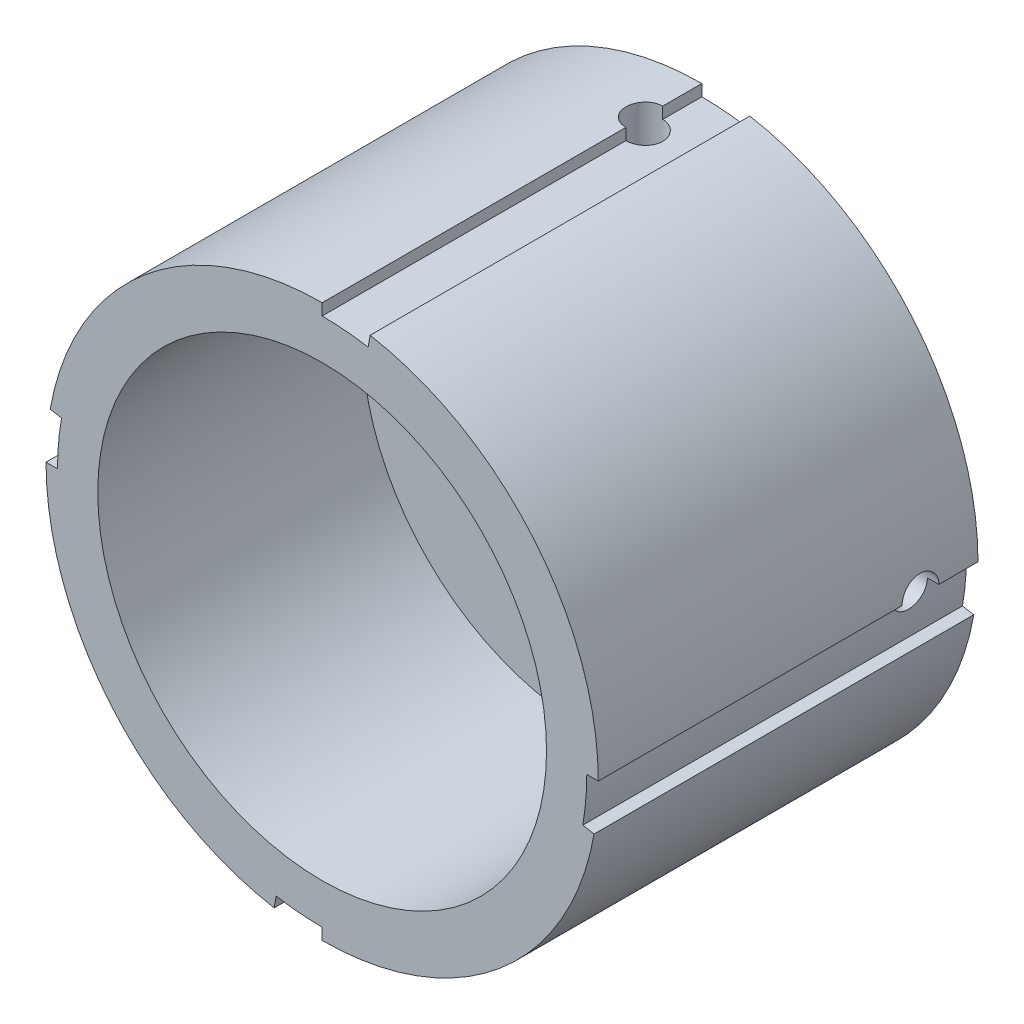
SolidWorks part; units mm, degrees
ref_plane "Alzado" through (0, 0, 0) normal (0, 0, 1) x (1, 0, 0)
ref_plane "Planta" through (0, 0, 0) normal (0, 1, 0) x (1, 0, 0)
ref_plane "Vista lateral" through (0, 0, 0) normal (1, 0, 0) x (0, 0, -1)
sketch "Croquis1" plane through (0, 0, 0) normal (0, 0, 1) x (1, 0, 0)
  line L0 (0, 0) -> (0, 24) construction
  line L1 (0, 24) -> (0, 23)
  line L2 (3.9939, 22.6506) -> (4.1676, 23.6354)
  line L3 (24, 0) -> (23, 0)
  line L4 (22.6506, -3.9939) -> (23.6354, -4.1676)
  line L5 (0, -24) -> (0, -23)
  line L6 (-3.9939, -22.6506) -> (-4.1676, -23.6354)
  line L7 (-24, 0) -> (-23, 0)
  line L8 (-22.6506, 3.9939) -> (-23.6354, 4.1676)
  line L9 (0, 0) -> (3.9939, 22.6506) construction
  arc A1 (3.9939, 22.6506) -> (0, 23) centre (0, 0) ccw
  arc A3 (22.6506, -3.9939) -> (23, 0) centre (0, 0) ccw
  arc A5 (-3.9939, -22.6506) -> (0, -23) centre (0, 0) ccw
  arc A7 (-22.6506, 3.9939) -> (-23, 0) centre (0, 0) ccw
  arc A8 (0, 24) -> (-23.6354, 4.1676) centre (0, 0) ccw
  arc A9 (24, 0) -> (4.1676, 23.6354) centre (0, 0) ccw
  arc A10 (0, -24) -> (23.6354, -4.1676) centre (0, 0) ccw
  arc A11 (-24, 0) -> (-4.1676, -23.6354) centre (0, 0) ccw
  circle A12 centre (0, 0) radius 23 construction
  point P20 (0, 0)
  dimension "D1" = 24
  dimension "D2" = 46
  dimension "D6" = 46
  dimension "D3" = 10
  dimension "D5" = 4
extrude "Saliente-Extruir1" add sketch "Croquis1" along normal mid plane 33
sketch "Croquis2" plane through (0, 0, 16.5) normal (0, 0, 1) x (1, 0, 0)
  circle A0 centre (0, 0) radius 19.5
  dimension "D1" = 39
extrude "Cortar-Extruir1" cut sketch "Croquis2" against normal blind 23
sketch "Croquis3" plane through (0, 0, -16.5) normal (0, 0, -1) x (-1, 0, 0)
  line L0 (-1.0308, 2) -> (1.0308, 2)
  circle A0 centre (0, 0) radius 2.25
  dimension "D1" = 4.5
  dimension "D2" = 2
extrude "Cortar-Extruir2" cut sketch "Croquis3" against normal blind 23 contours L0 A0
sketch "Croquis4" plane through (0, 0, 0) normal (0, 1, 0) x (1, 0, 0)
  line L0 (0, -20.7543) -> (0, 35.0478) construction
  line L1 (0, -16.5) -> (0, 16.5) construction
  line L2 (0, 16.5) -> (-23.6354, 16.5) construction
  circle A0 centre (0, 11.5) radius 1.6
  dimension "D1" = 3.2
  dimension "D2" = 5
extrude "Cortar-Extruir3" cut sketch "Croquis4" against normal mid plane 73
sketch "Croquis5" plane through (0, 0, 0) normal (1, 0, 0) x (0, 0, -1)
  line L0 (0, 0) -> (11.5, 0) construction
  line L1 (16.5, 0) -> (16.5, 23.6354) construction
  circle A0 centre (11.5, 0) radius 1.6
  dimension "D2" = 3.2
  dimension "D1" = 5
extrude "Cortar-Extruir4" cut sketch "Croquis5" against normal mid plane 283
sketch "Croquis6" plane through (0, 0, -16.5) normal (0, 0, -1) x (-1, 0, 0)
  line L0 (0, -25.9532) -> (0, 54.6675) construction
  line L1 (56.1694, 0) -> (-55.2683, 0) construction
  line L3 (-2.75, 9.4) -> (2.75, 9.4)
  line L4 (-2.75, 9.4) -> (-2.75, 7)
  line L5 (-2.75, 7) -> (2.75, 7)
  line L6 (2.75, 9.4) -> (2.75, 7)
  line L7 (8, 2.75) -> (10.4, 2.75)
  line L8 (8, 2.75) -> (8, -2.75)
  line L9 (8, -2.75) -> (10.4, -2.75)
  line L10 (10.4, 2.75) -> (10.4, -2.75)
  line L11 (-1.0308, 2) -> (1.0308, 2) construction
  dimension "D1" = 2.4
  dimension "D2" = 5.5
  dimension "D3" = 5.5
  dimension "D4" = 2.4
  dimension "D5" = 7
  dimension "D6" = 8
  dimension "D7" = 5
extrude "Cortar-Extruir5" cut sketch "Croquis6" against normal blind 283
